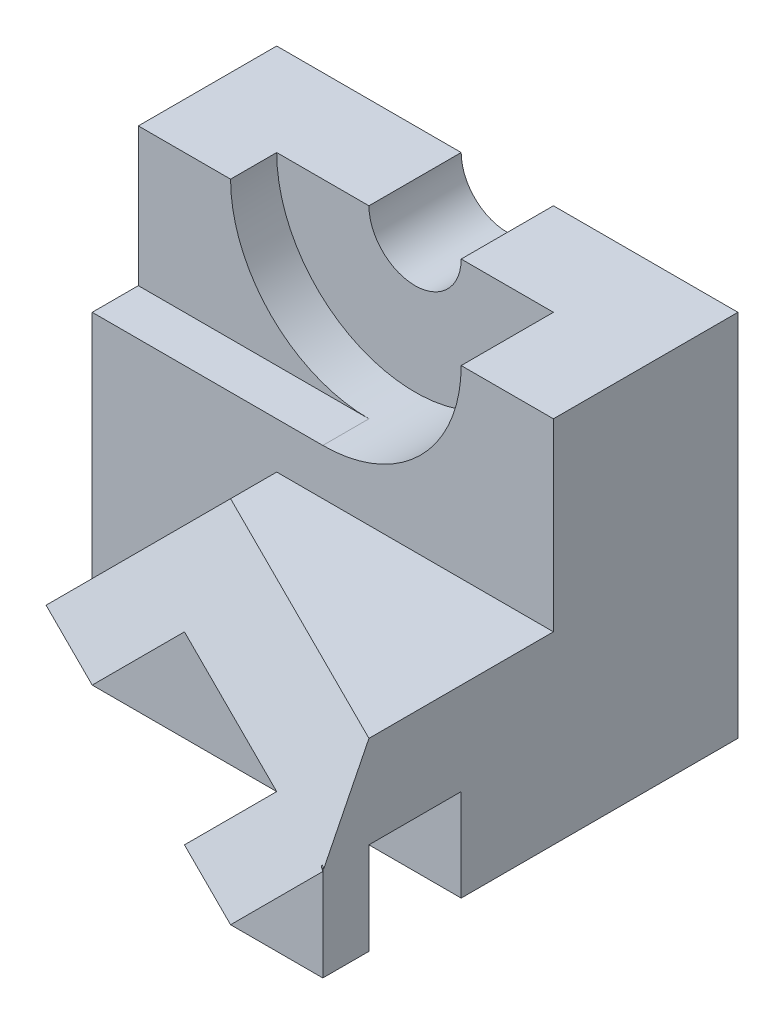
SolidWorks part; units mm, degrees
ref_plane "Front Plane" through (0, 0, 0) normal (0, 0, 1) x (1, 0, 0)
ref_plane "Top Plane" through (0, 0, 0) normal (0, 1, 0) x (1, 0, 0)
ref_plane "Right Plane" through (0, 0, 0) normal (1, 0, 0) x (0, 0, -1)
sketch "Sketch1" plane through (0, 0, 0) normal (0, 0, 1) x (1, 0, 0)
  line L1 (0, 0) -> (100, 0)
  line L2 (0, 0) -> (0, 80)
  line L3 (0, 80) -> (100, 80)
  line L4 (100, 0) -> (100, 80)
  dimension "D1" = 100
  dimension "D2" = 80
extrude "Boss-Extrude1" add sketch "Sketch1" along normal blind 90
sketch "Sketch3" plane through (0, 80, 0) normal (0, 1, 0) x (1, 0, 0)
  line L0 (0, -50) -> (20, -60)
  line L1 (0, -90) -> (0, 0) construction
  line L2 (20, -60) -> (40, -60)
  line L3 (40, -60) -> (80, -80)
  line L4 (80, -80) -> (60, -80)
  line L5 (60, -80) -> (80, -90)
  line L6 (100, -90) -> (0, -90) construction
  line L7 (80, -90) -> (0, -90)
  line L8 (0, -90) -> (0, -50)
  dimension "D1" = 20
  dimension "D2" = 10
  dimension "D3" = 20
  dimension "D4" = 20
  dimension "D5" = 40
  dimension "D6" = 20
extrude "Cut-Extrude1" cut sketch "Sketch3" against normal blind 90
sketch "Sketch4" plane through (100, 0, 0) normal (1, 0, 0) x (0, 0, -1)
  line L0 (-90, 0) -> (0, 0) construction
  line L1 (-80, 0) -> (-60, 0)
  line L2 (-80, 0) -> (-80, 20)
  line L3 (-80, 20) -> (-60, 20)
  line L4 (-60, 0) -> (-60, 20)
  dimension "D1" = 20
  dimension "D2" = 10
  dimension "D3" = 20
extrude "Cut-Extrude2" cut sketch "Sketch4" against normal blind 90
sketch "Sketch5" plane through (0, 0, 0) normal (0, 0, -1) x (-1, 0, 0)
  line L0 (-100, 80) -> (0, 80) construction
  line L1 (-60, 80) -> (-40, 80)
  arc A0 (-60, 80) -> (-40, 80) centre (-50, 80) ccw
  dimension "D1" = 10
  dimension "D2" = 40
extrude "Cut-Extrude3" cut sketch "Sketch5" against normal blind 90
ref_plane "Plane1" through (0, 0, 20) normal (0, 0, 1) x (1, 0, 0)
sketch "Sketch6" plane through (0, 0, 20) normal (0, 0, 1) x (1, 0, 0)
  line L0 (20, 80) -> (80, 80)
  arc A0 (80, 80) -> (20, 80) centre (50, 80) cw
  point P4 (40, 80)
  point P6 (60, 80)
  point P7 (60, 80)
  dimension "D1" = 30
  dimension "D2" = 20
extrude "Cut-Extrude4" cut sketch "Sketch6" along normal blind 90
ref_plane "Plane2" through (0, 0, 40) normal (0, 0, 1) x (1, 0, 0)
sketch "Sketch7" plane through (0, 0, 40) normal (0, 0, 1) x (1, 0, 0)
  line L1 (100, 80) -> (0, 80)
  line L2 (100, 80) -> (100, 40)
  line L3 (100, 40) -> (0, 40)
  line L4 (0, 80) -> (0, 40)
  point P4 (100, 80)
  dimension "D1" = 40
  dimension "D2" = 0
  dimension "D3" = 0
  dimension "D4" = 100
extrude "Cut-Extrude5" cut sketch "Sketch7" along normal blind 90
sketch "Sketch8" plane through (0, 0, 40) normal (0, 0, 1) x (1, 0, 0)
  line L0 (50, 50) -> (0, 50)
  line L1 (0, 80) -> (0, 40) construction
  line L2 (0, 50) -> (0, 80)
  line L3 (0, 80) -> (20, 80)
  arc A0 (20, 80) -> (50, 50) centre (50, 80) ccw
extrude "Cut-Extrude6" cut sketch "Sketch8" against normal blind 10
sketch "Sketch9" plane through (0, 0, 40) normal (0, 0, 1) x (1, 0, 0)
  line L0 (40, 40) -> (0, 0)
  line L1 (0, 40) -> (100, 40) construction
  line L2 (0, 0) -> (0, 40)
  line L3 (0, 40) -> (40, 40)
  dimension "D1" = 40
extrude "Cut-Extrude7" cut sketch "Sketch9" along normal blind 94
ref_plane "Plane3" through (0, 0, 50) normal (0, 0, 1) x (1, 0, 0)
sketch "Sketch10" plane through (0, 0, 50) normal (0, 0, 1) x (1, 0, 0)
  line L1 (0, 0) -> (100, 0)
  line L2 (0, 0) -> (0, 50)
  line L3 (0, 50) -> (100, 50)
  line L4 (100, 0) -> (100, 50)
  dimension "D1" = 100
  dimension "D2" = 0
extrude "Cut-Extrude8" cut sketch "Sketch10" along normal blind 94
sketch "Sketch11" plane through (0, 40, 0) normal (0, 1, 0) x (1, 0, 0)
  line L0 (100, -50) -> (100, -80)
  line L1 (100, -80) -> (40, -50)
  line L2 (40, -50) -> (100, -50)
  dimension "D1" = 30
extrude "Boss-Extrude2" add sketch "Sketch11" against normal blind 40
sketch "Sketch15" plane through (0, 0, 50) normal (0, 0, 1) x (1, 0, 0)
  line L0 (20, 0) -> (40, 20)
  line L1 (0, 0) -> (40, 0) construction
  line L2 (40, 20) -> (100, 20)
  line L3 (40, 0) -> (100, 0)
  line L4 (100, 0) -> (100, 20)
  line L8 (0, 0) -> (40, 0)
  line L9 (40, 0) -> (40, 40)
  line L10 (40, 40) -> (0, 0)
  line L11 (20, 0) -> (40, 0)
  dimension "D1" = 20
  dimension "D2" = 20
  dimension "D3" = 20
  dimension "D4" = 0
  dimension "D5" = 0
  dimension "D6" = 0
extrude "Boss-Extrude4" add sketch "Sketch15" along normal blind 10
ref_plane "Plane6" through (-16.6667, 16.6667, 33.3333) normal (0.4082, -0.4082, -0.8165) x (-0.9129, -0.1826, -0.3651)
sketch "Sketch16" plane through (-16.6667, 16.6667, 33.3333) normal (0.4082, -0.4082, -0.8165) x (-0.9129, -0.1826, -0.3651)
  line L0 (-62.0752, -8.9443) -> (-42.0752, -2.9135)
  line L1 (-62.0752, 13.4164) -> (-18.2574, -22.3607) construction
  line L2 (-42.0752, -2.9135) -> (-18.2574, -22.3607)
  line L3 (-18.2574, -22.3607) -> (-40.1663, -26.8328)
  line L4 (-40.1663, -26.8328) -> (-62.0752, -8.9443)
  dimension "D1" = 20
extrude "Boss-Extrude5" add sketch "Sketch16" along normal blind 10
ref_plane "Plane7" through (1.303, 13.6515, -2.6059) normal (-0.0933, -0.978, 0.1867) x (-0.9956, 0.0917, -0.0175)
sketch "Sketch18" plane through (0, 20, 0) normal (0, 1, 0) x (1, 0, 0)
  line L0 (40, -50) -> (40, -60)
  line L1 (40, -60) -> (21.7426, -50)
  line L2 (21.7426, -50) -> (40, -50)
extrude "Boss-Extrude9" add sketch "Sketch18" against normal blind 10
sketch "Sketch19" plane through (100, 0, 0) normal (1, 0, 0) x (0, 0, -1)
  line L0 (-80, 0) -> (-80, 40) construction
  point P0 (-90, 20)
  point P1 (-80, 20)
  dimension "D1" = 20
  dimension "D2" = 10
ref_plane "Plane9" through (40, 0, 0) normal (1, 0, 0) x (0, 0, -1)
sketch "Sketch22" plane through (40, 0, 0) normal (1, 0, 0) x (0, 0, -1)
  line L1 (-50, 20) -> (-63.6458, 20)
  line L2 (-50, 20) -> (-50, 39.7516)
  line L3 (-50, 39.7516) -> (-63.6458, 39.7516)
  line L4 (-63.6458, 20) -> (-63.6458, 39.7516)
  dimension "D1" = 13.6458
  dimension "D2" = 19.7516
extrude "Cut-Extrude12" cut sketch "Sketch22" against normal blind 57
ref_plane "Plane10" through (0, 20, 0) normal (0, 1, 0) x (1, 0, 0)
sketch "Sketch23" plane through (0, 20, 0) normal (0, 1, 0) x (1, 0, 0)
  line L0 (20, -50) -> (100, -90)
  line L1 (100, -90) -> (40, -50)
  line L2 (40, -50) -> (20, -50)
extrude "Boss-Extrude13" add sketch "Sketch23" against normal blind 20
sketch "Sketch24" plane through (0, 20, 0) normal (0, 1, 0) x (1, 0, 0)
  line L0 (100, -90) -> (100, -80)
  line L1 (100, -80) -> (60, -60)
  line L2 (60, -60) -> (55, -60)
  line L3 (55, -60) -> (100, -90)
extrude "Boss-Extrude14" add sketch "Sketch24" against normal blind 20
sketch "Sketch25" plane through (100, 0, 0) normal (1, 0, 0) x (0, 0, -1)
  line L0 (-90, 0) -> (0, 0) construction
  line L1 (-90, 20) -> (-80, 20)
  line L2 (-90, 20) -> (-90, 0)
  line L3 (-90, 0) -> (-80, 0)
  line L4 (-80, 20) -> (-80, 0)
  dimension "D1" = 10
extrude "Boss-Extrude16" add sketch "Sketch25" against normal blind 40
ref_plane "Plane11" through (-16.6667, 16.6667, 33.3333) normal (-0.4082, 0.4082, 0.8165) x (0.9129, 0.1826, 0.3651)
sketch "Sketch26" plane through (-16.6667, 16.6667, 33.3333) normal (-0.4082, 0.4082, 0.8165) x (0.9129, 0.1826, 0.3651)
  line L0 (105.893, -17.8885) -> (83.9841, -35.7771)
  line L1 (83.9841, -35.7771) -> (105.893, -40.2492)
  line L2 (105.893, -40.2492) -> (105.893, -17.8885)
  line L3 (87.6356, -40.2492) -> (124.1504, -40.2492) construction
extrude "Cut-Extrude13" cut sketch "Sketch26" along normal blind 40
sketch "Sketch27" plane through (-3.3333, -16.6667, 6.6667) normal (0.1826, 0.9129, -0.3651) x (0.9832, -0.1695, 0.0678)
  line L0 (64.416, -74.2781) -> (84.7579, -83.5629)
  line L1 (84.7579, -83.5629) -> (64.416, -85.0485)
  line L2 (64.416, -85.0485) -> (64.416, -74.2781)
extrude "Cut-Extrude14" cut sketch "Sketch27" against normal blind 40
sketch "Sketch28" plane through (0, 0, 80) normal (0, 0, -1) x (-1, 0, 0)
  line L0 (-80, 20) -> (-60, 0)
  line L1 (-60, 0) -> (-60, 20)
  line L2 (-60, 20) -> (-80, 20)
extrude "Cut-Extrude15" cut sketch "Sketch28" against normal blind 40
ref_plane "Plane12" through (-16.6667, 16.6667, 33.3333) normal (0.4082, -0.4082, -0.8165) x (-0.9129, -0.1826, -0.3651)
sketch "Sketch29" plane through (-16.6667, 16.6667, 33.3333) normal (0.4082, -0.4082, -0.8165) x (-0.9129, -0.1826, -0.3651)
  line L0 (-105.893, -17.8885) -> (-105.893, -40.2492)
  line L1 (-105.893, -40.2492) -> (-127.8019, -22.3607)
  line L2 (-127.8019, -22.3607) -> (-105.893, -17.8885)
extrude "Cut-Extrude16" cut sketch "Sketch29" against normal blind 40
sketch "Sketch30" plane through (100, 0, 0) normal (1, 0, 0) x (0, 0, -1)
  line L0 (-90, 0) -> (0, 0) construction
  line L1 (-80, 19.999) -> (-60, 19.999)
  line L2 (-80, 19.999) -> (-80, 0)
  line L3 (-80, 0) -> (-60, 0)
  line L4 (-60, 19.999) -> (-60, 0)
  dimension "D1" = 20
  dimension "D2" = 10
  dimension "D3" = 19.999
extrude "Cut-Extrude18" cut sketch "Sketch30" against normal blind 125
sketch "Sketch31" plane through (0, 20, 0) normal (0, 1, 0) x (1, 0, 0)
  line L0 (40, -50) -> (20, -50)
  line L1 (20, -50) -> (100, -90)
  line L2 (100, -90) -> (100, -80)
  line L3 (100, -80) -> (40, -50)
extrude "Boss-Extrude25" add sketch "Sketch31" along normal blind 0.5
ref_plane "Plane15" through (-16.6667, 16.6667, 33.3333) normal (-0.4082, 0.4082, 0.8165) x (0.9129, 0.1826, 0.3651)
sketch "Sketch34" plane through (-16.6667, 16.6667, 33.3333) normal (-0.4082, 0.4082, 0.8165) x (0.9129, 0.1826, 0.3651)
  line L0 (40.1663, -4.4721) -> (127.8019, -22.3607)
  line L1 (127.8019, -22.3607) -> (94.9386, 6.7082)
  line L2 (62.0752, 13.4164) -> (127.8019, 0) construction
  line L3 (94.9386, 6.7082) -> (40.1663, -4.4721)
  line L4 (18.2574, -22.3607) -> (40.1663, -4.4721) construction
extrude "Cut-Extrude21" cut sketch "Sketch34" along normal blind 0.5
sketch "Sketch35" plane through (2.2667, -10.4267, 6.3467) normal (0.1826, -0.8398, 0.5112) x (0.9832, 0.156, -0.0949)
  line L0 (19.0112, 53.7781) -> (19.3079, 53.6892)
  line L1 (19.3079, 53.6892) -> (18.0365, 53.1089)
  line L2 (18.0365, 53.1089) -> (19.0112, 53.7781)
extrude "Cut-Extrude22" cut sketch "Sketch35" against normal blind 2.5
sketch "Sketch36" plane through (0, 0, 0) normal (-0.7071, 0.7071, 0) x (0, 0, 1)
  line L0 (50, 56.5685) -> (50, 28.9914) construction
  line L1 (50, 31.0655) -> (48.8513, 31.0655)
  line L2 (50, 31.0655) -> (50, 27.0586)
  line L3 (50, 27.0586) -> (48.8513, 27.0586)
  line L4 (48.8513, 31.0655) -> (48.8513, 27.0586)
  dimension "D1" = 1.1487
  dimension "D2" = 4.007
  dimension "D3" = 1.7955
extrude "Boss-Extrude26" add sketch "Sketch36" against normal blind 2.5
sketch "Sketch37" plane through (0, 0, 50) normal (0, 0, -1) x (-1, 0, 0)
  line L0 (-20, 20) -> (-20.3058, 20.5)
  line L1 (-20.3058, 20.5) -> (-20, 20.5)
  line L2 (-20, 20.5) -> (-20, 20)
extrude "Cut-Extrude23" cut sketch "Sketch37" against normal blind 2.5
sketch "Sketch39" plane through (-18.6839, 11.4264, 25.4447) normal (0.5565, -0.3404, -0.7579) x (-0.8308, -0.228, -0.5077)
  line L0 (-46.9288, -1.7819) -> (-47.7143, -1.9782)
  line L2 (-46.9288, -1.7819) -> (-46.5608, -2.238)
  line L3 (-46.5608, -2.238) -> (-47.7143, -1.9782)
extrude "Cut-Extrude24" cut sketch "Sketch39" against normal blind 2.5
sketch "Sketch40" plane through (0, 0, 0) normal (0, -1, 0) x (1, 0, 0)
  line L1 (0, 0) -> (100, 0)
  line L2 (0, 0) -> (0, 60)
  line L3 (0, 60) -> (100, 60)
  line L4 (100, 0) -> (100, 60)
extrude "Cut-Extrude25" cut sketch "Sketch40" along normal blind 39.5
ref_plane "Plane16" through (-16.6667, 16.6667, 33.3333) normal (-0.4082, 0.4082, 0.8165) x (0.9129, 0.1826, 0.3651)
sketch "Sketch41" plane through (-16.6667, 16.6667, 33.3333) normal (-0.4082, 0.4082, 0.8165) x (0.9129, 0.1826, 0.3651)
  line L0 (40.1663, -4.4721) -> (62.0752, 13.4164)
  line L1 (62.0752, 13.4164) -> (127.8019, 0)
  line L2 (127.8019, 0) -> (127.8019, -22.3607)
  line L3 (127.8019, -22.3607) -> (40.1663, -4.4721)
extrude "Boss-Extrude31" add sketch "Sketch41" against normal blind 80
sketch "Sketch45" plane through (100, 0, 0) normal (1, 0, 0) x (0, 0, -1)
  line L1 (0, 80) -> (-90, 80)
  line L2 (0, 80) -> (0, 0)
  line L3 (0, 0) -> (-90, 0)
  line L4 (-90, 80) -> (-90, 0)
extrude "Cut-Extrude27" cut sketch "Sketch45" along normal blind 80
sketch "Sketch46" plane through (0, 0, 0) normal (0, -1, 0) x (1, 0, 0)
  line L1 (0, 50) -> (100, 50)
  line L2 (0, 50) -> (0, 0)
  line L3 (0, 0) -> (100, 0)
  line L4 (100, 50) -> (100, 0)
extrude "Cut-Extrude28" cut sketch "Sketch46" along normal blind 80
sketch "Sketch47" plane through (0, 0, 0) normal (0, 1, 0) x (1, 0, 0)
  line L0 (120, -50) -> (100, -40)
  line L1 (100, -40) -> (100, -2.0204)
  line L2 (100, -2.0204) -> (132.6599, -18.3503)
  line L3 (132.6599, -18.3503) -> (120, -50)
extrude "Cut-Extrude29" cut sketch "Sketch47" against normal blind 80
sketch "Sketch48" plane through (120.6897, 0, 48.2759) normal (-0.9285, 0, -0.3714) x (-0.3714, 0, 0.9285)
  line L0 (-32.2308, 0) -> (1.857, 0)
  line L1 (1.857, 0) -> (-26.5495, -12.6599)
  line L2 (-26.5495, -12.6599) -> (-32.2308, 0)
extrude "Cut-Extrude30" cut sketch "Sketch48" against normal blind 80
sketch "Sketch49" plane through (-0.1143, -0.6904, 0.2857) normal (0.1512, 0.9134, -0.378) x (0.9885, -0.1397, 0.0578)
  line L0 (121.5109, -46.2008) -> (134.318, -17.9587)
  line L1 (134.318, -17.9587) -> (132.1835, -16.9896)
  line L2 (132.1835, -16.9896) -> (121.5109, -46.2008)
  line L3 (102.3189, -55.441) -> (98.8506, 0) construction
  line L4 (134.318, -17.9587) -> (119.4148, -17.9587)
  line L5 (134.318, -17.9587) -> (134.318, -48.4393)
  line L6 (134.318, -48.4393) -> (119.4148, -48.4393)
  line L7 (119.4148, -17.9587) -> (119.4148, -48.4393)
  line M4 (121.5109, -46.2008) -> (134.318, -17.9587)
  dimension "D1" = 14.9033
  dimension "D2" = 19.4028
  dimension "D3" = 30.4806
extrude "Cut-Extrude32" cut sketch "Sketch49" against normal blind 80 contours L4 L7 L6 L5 L2 M4
sketch "Sketch51" plane through (0.6667, 3.3333, -1.3333) normal (-0.1826, -0.9129, 0.3651) x (-0.9832, 0.1695, -0.0678)
  line L0 (-102.3876, -55.7086) -> (-98.3192, 0) construction
  line L1 (-143.6139, 253.0441) -> (-118.4832, 253.0441)
  line L2 (-143.6139, 253.0441) -> (-143.6139, -46.9559)
  line L3 (-143.6139, -46.9559) -> (-118.4832, -46.9559)
  line L4 (-118.4832, 253.0441) -> (-118.4832, -46.9559)
  dimension "D1" = 300
  dimension "D2" = 25.1307
  dimension "D3" = 16.6904
  dimension "D4" = 255.7701
extrude "Cut-Extrude33" cut sketch "Sketch51" against normal blind 80
sketch "Sketch52" plane through (0, 0, 0) normal (0, 0, -1) x (-1, 0, 0)
  line L1 (0, 80) -> (-100, 80)
  line L2 (0, 80) -> (0, 0)
  line L3 (0, 0) -> (-100, 0)
  line L4 (-100, 80) -> (-100, 0)
extrude "Cut-Extrude34" cut sketch "Sketch52" along normal blind 80
sketch "Sketch53" plane through (0, 0, 0) normal (0, 0, 1) x (1, 0, 0)
  line L0 (100, 8) -> (100, 4.0408)
  line L1 (100, 4.0408) -> (103.2993, 7.3401)
  line L2 (103.2993, 7.3401) -> (100, 8)
extrude "Cut-Extrude35" cut sketch "Sketch53" against normal blind 80
sketch "Sketch54" plane through (0, 0, 0) normal (0, 1, 0) x (1, 0, 0)
  line L0 (50, 0) -> (95.9592, 0)
  line L1 (95.9592, 0) -> (65.3197, 15.3197)
  line L2 (65.3197, 15.3197) -> (50, 0)
extrude "Cut-Extrude36" cut sketch "Sketch54" against normal blind 80
sketch "Sketch55" plane through (25, 0, 25) normal (0.7071, 0, 0.7071) x (0.7071, 0, -0.7071)
  line L0 (35.3553, 0) -> (35.3553, -6)
  line L1 (35.3553, -6) -> (51.0528, -12.6599)
  line L2 (51.0528, -12.6599) -> (57.0207, 0)
  line L3 (57.0207, 0) -> (35.3553, 0)
extrude "Cut-Extrude37" cut sketch "Sketch55" against normal blind 80
sketch "Sketch56" plane through (2.2881, 7.6271, -2.2881) normal (0.2762, 0.9206, -0.2762) x (0.9611, -0.2645, 0.0794)
  line L1 (46.5212, 4.5976) -> (63.1385, 4.5976)
  line L2 (46.5212, 4.5976) -> (46.5212, 18.8714)
  line L3 (46.5212, 18.8714) -> (63.1385, 18.8714)
  line L4 (63.1385, 4.5976) -> (63.1385, 18.8714)
  dimension "D1" = 16.6174
  dimension "D2" = 14.2738
extrude "Cut-Extrude38" cut sketch "Sketch56" against normal blind 80
sketch "Sketch57" plane through (0, 0, 0) normal (0, 0, -1) x (-1, 0, 0)
  line L0 (0, 80) -> (0, 0) construction
  line L1 (0, 13.7177) -> (-100.1952, 13.7177)
  line L2 (0, 13.7177) -> (0, -43.4402)
  line L3 (0, -43.4402) -> (-100.1952, -43.4402)
  line L4 (-100.1952, 13.7177) -> (-100.1952, -43.4402)
  dimension "D1" = 57.1579
  dimension "D2" = 100.1952
  dimension "D3" = 100.1952
  dimension "D4" = 13.7177
extrude "Cut-Extrude39" cut sketch "Sketch57" along normal blind 80
sketch "Sketch58" plane through (100, 0, 0) normal (1, 0, 0) x (0, 0, -1)
  line L1 (-80, 0) -> (-60, 0)
  line L2 (-80, 0) -> (-80, 20)
  line L3 (-80, 20) -> (-60, 20)
  line L4 (-60, 0) -> (-60, 20)
  dimension "D1" = 20
  dimension "D2" = 20
extrude "Cut-Extrude40" cut sketch "Sketch58" against normal blind 80
